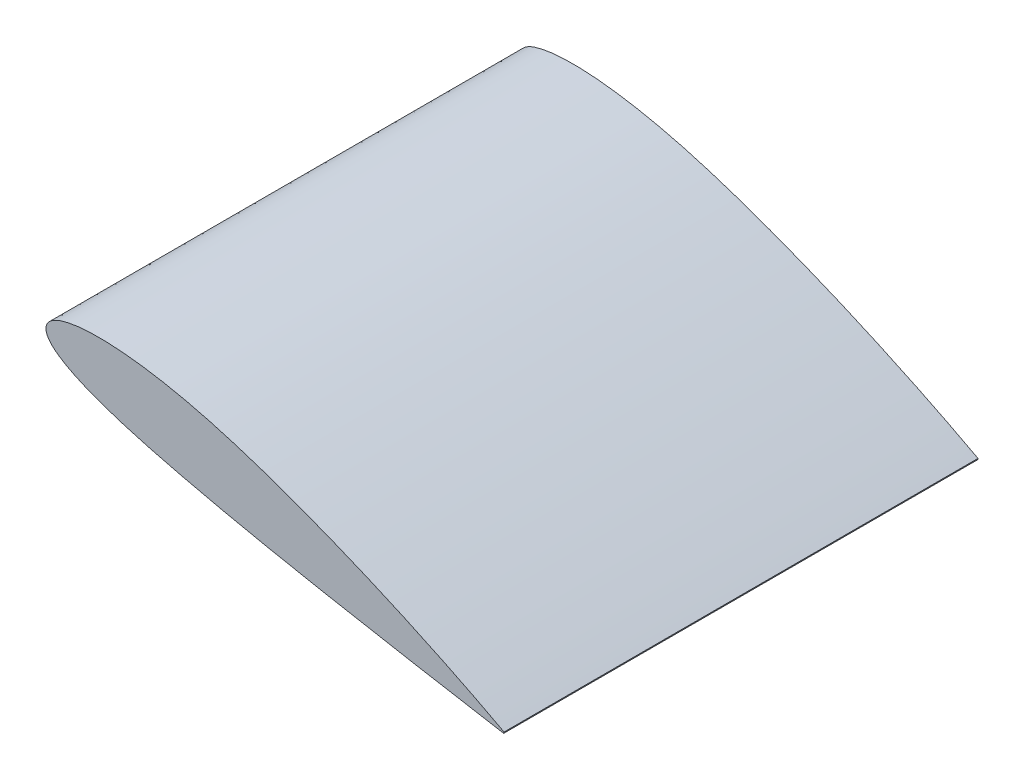
SolidWorks part; units mm, degrees
ref_plane "Front Plane"
ref_plane "Top Plane" through (0, 0, 0) normal (0, 1, 0) x (1, 0, 0)
ref_plane "Right Plane" through (0, 0, 0) normal (1, 0, 0) x (0, 0, -1)
curve "Krzywa1"
  spline degree 3 poles (1, 0.0015, 0) (0.9991, 0.0017, 0) (0.9956, 0.0025, 0) (0.9875, 0.0044, 0) (0.9742, 0.0074, 0) (0.9556, 0.0115, 0) (0.9322, 0.0166, 0) (0.904, 0.0224, 0) (0.8713, 0.0289, 0) (0.8346, 0.0358, 0) (0.7942, 0.043, 0) (0.7505, 0.0503, 0) (0.7041, 0.0574, 0) (0.6553, 0.0643, 0) (0.6048, 0.0707, 0) (0.5531, 0.0765, 0) (0.5007, 0.0814, 0) (0.4483, 0.0853, 0) (0.3962, 0.0881, 0) (0.3451, 0.0894, 0) (0.2956, 0.089, 0) (0.2483, 0.0868, 0) (0.2039, 0.083, 0) (0.1628, 0.0776, 0) (0.1256, 0.0708, 0) (0.0927, 0.0627, 0) (0.0643, 0.0537, 0) (0.0409, 0.0439, 0) (0.0225, 0.0337, 0) (0.0093, 0.0231, 0) (0.0011, 0.0119, 0) (-0.001, -0.0001, 0) (0.0034, -0.0114, 0) (0.0135, -0.0208, 0) (0.0284, -0.0287, 0) (0.0479, -0.0355, 0) (0.0722, -0.0411, 0) (0.1009, -0.0456, 0) (0.1337, -0.0489, 0) (0.1703, -0.0511, 0) (0.2104, -0.0521, 0) (0.2535, -0.0522, 0) (0.2992, -0.0514, 0) (0.347, -0.0499, 0) (0.3967, -0.0479, 0) (0.4476, -0.0455, 0) (0.4993, -0.0424, 0) (0.5511, -0.0389, 0) (0.6024, -0.0352, 0) (0.6526, -0.0314, 0) (0.7012, -0.0275, 0) (0.7477, -0.0237, 0) (0.7915, -0.0201, 0) (0.8321, -0.0166, 0) (0.8691, -0.0134, 0) (0.9021, -0.0105, 0) (0.9307, -0.0079, 0) (0.9546, -0.0057, 0) (0.9734, -0.004, 0) (0.9871, -0.0027, 0) (0.9953, -0.0019, 0) (0.999, -0.0016, 0) (1, -0.0015, 0) knots 0 0 0 0 0.001308 0.005358 0.012063 0.021337 0.033087 0.047171 0.063441 0.081714 0.101785 0.123442 0.146433 0.170517 0.195424 0.220875 0.246594 0.272302 0.297725 0.322799 0.347029 0.370162 0.391954 0.412188 0.43067 0.447231 0.461732 0.474085 0.484276 0.492392 0.498749 0.5041 0.509453 0.51579 0.523838 0.533885 0.546005 0.560171 0.576284 0.594211 0.613803 0.634869 0.65721 0.680611 0.704835 0.729853 0.755197 0.780583 0.805729 0.830359 0.854204 0.877002 0.898494 0.918443 0.936623 0.952826 0.966868 0.978592 0.987852 0.994547 0.998596 1 1 1 1
sketch "Szkic1" plane through (0, 0, 0) normal (0, 0, 1) x (1, 0, 0)
  line L0 (500, -0.735) -> (500.3805, 0.6849)
  spline S1 degree 3 poles (500.3805, 0.6849) (499.9878, 0.8995) (498.3795, 1.7782) (494.7248, 3.6934) (488.6686, 6.8947) (480.2539, 11.2694) (469.5724, 16.7545) (451.1247, 26.0351) (423.3303, 39.5479) (385.0202, 57.2211) (349.3242, 72.6684) (318.4708, 85.2641) (294.2362, 94.7399) (269.5814, 103.8825) (244.7699, 112.5628) (219.9932, 120.6607) (195.479, 127.9071) (171.4875, 134.109) (148.3802, 139.1848) (126.4304, 143.0784) (105.9053, 145.7883) (87.0506, 147.2993) (70.0989, 147.6833) (55.2516, 146.9867) (42.6734, 145.3124) (32.4722, 142.7379) (24.7043, 139.3243) (19.3074, 134.9879) (16.7101, 129.468) (17.409, 123.4191) (21.0763, 117.5905) (27.2124, 111.8519) (35.7912, 106.0384) (46.7651, 100.1761) (60.0356, 94.3051) (75.4577, 88.4574) (92.871, 82.677) (112.0843, 76.9805) (132.8882, 71.3638) (155.0601, 65.8352) (178.357, 60.3663) (202.5974, 54.9149) (227.5279, 49.5061) (252.9064, 44.2947) (278.3665, 39.2692) (311.6203, 32.8751) (351.2721, 25.518) (389.2029, 18.631) (422.4093, 12.7069) (445.4376, 8.6349) (465.708, 5.122) (477.513, 3.0836) (486.8457, 1.4943) (493.5901, 0.3447) (497.6895, -0.3332) (499.5268, -0.6527) (500, -0.735) knots 0 0 0 0 0.001308 0.005358 0.012063 0.021337 0.033087 0.047171 0.081714 0.123442 0.170517 0.195424 0.220875 0.246594 0.272302 0.297725 0.322799 0.347029 0.370162 0.391954 0.412188 0.43067 0.447231 0.461732 0.474085 0.484276 0.492392 0.498749 0.5041 0.509453 0.51579 0.523838 0.533885 0.546005 0.560171 0.576284 0.594211 0.613803 0.634869 0.65721 0.680611 0.704835 0.729853 0.755197 0.780583 0.805729 0.854204 0.898494 0.918443 0.952826 0.966868 0.978592 0.987852 0.994547 0.998596 1 1 1 1
extrude "Dodanie-wyciągnięcie1" add sketch "Szkic1" along normal blind 500
